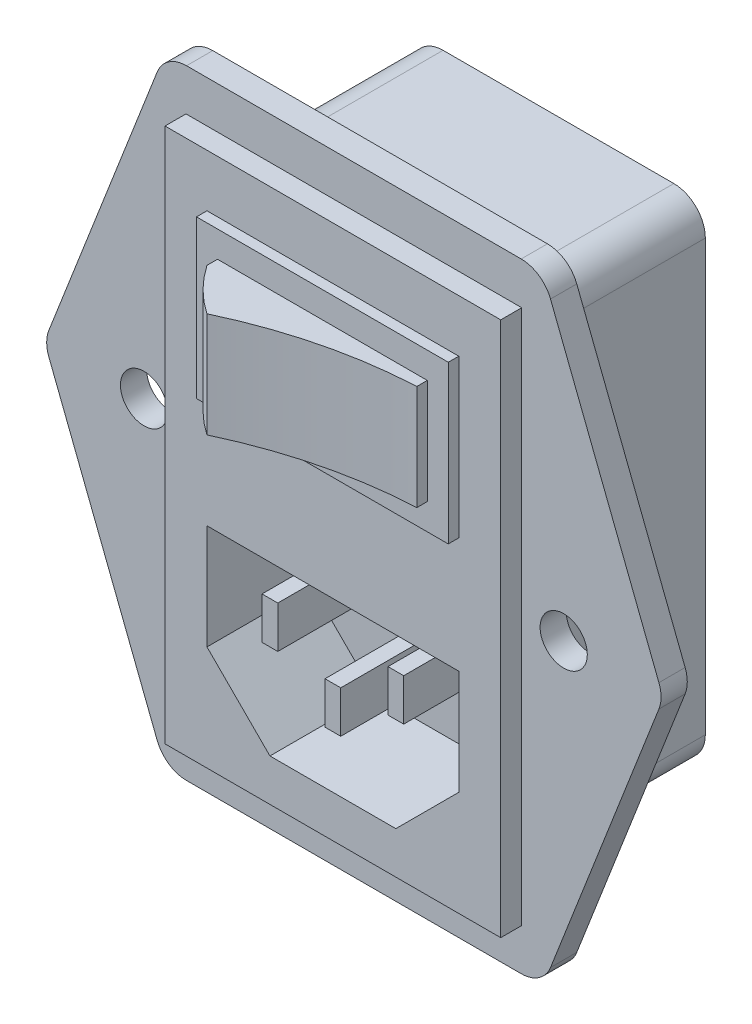
SolidWorks part; units mm, degrees
material "PBT Общее назначение"
ref_plane "Спереди" through (0, 0, 0) normal (0, 0, 1) x (1, 0, 0)
ref_plane "Сверху" through (0, 0, 0) normal (0, 1, 0) x (1, 0, 0)
ref_plane "Справа" through (0, 0, 0) normal (1, 0, 0) x (0, 0, -1)
sketch "Эскиз1" plane through (0, 0, 0) normal (0, 0, 1) x (1, 0, 0)
  line L0 (0, 0) -> (28, 0)
  line L1 (0, 0) -> (0, 47)
  line L2 (28, 0) -> (28, 47)
  line L3 (0, 47) -> (28, 47)
  dimension "D1" = 47
  dimension "D2" = 28
extrude "Бобышка-Вытянуть1" add sketch "Эскиз1" along normal blind 17
sketch "Эскиз2" plane through (0, 0, 17) normal (0, 0, 1) x (1, 0, 0)
  line L0 (14, 0) -> (14, 47) construction
  line L2 (0, 0) -> (28, 0) construction
  line L3 (28, 47) -> (0, 47) construction
  line L4 (-4, 53) -> (32, 53)
  line L5 (-4, 53) -> (-4, -6) construction
  line L6 (32, 53) -> (32, -6) construction
  line L7 (-4, -6) -> (32, -6)
  line L8 (-4, 53) -> (-15.5, 23.5)
  line L9 (-15.5, 23.5) -> (-4, -6)
  line L10 (14, 47) -> (14, 53) construction
  line L11 (43.5, 23.5) -> (32, -6)
  line L12 (32, 53) -> (43.5, 23.5)
  line L13 (0, 23.5) -> (28, 23.5) construction
  line L14 (0, 47) -> (0, 0) construction
  line L15 (28, 0) -> (28, 47) construction
  line L16 (-15.5, 23.5) -> (43.5, 23.5) construction
  line L17 (-4, 23.5) -> (32, 23.5) construction
  dimension "D1" = 59
  dimension "D2" = 59
  dimension "D3" = 6
  dimension "D4" = 4
extrude "Бобышка-Вытянуть2" add sketch "Эскиз2" along normal blind 2.5
sketch "Эскиз3" plane through (0, 0, 19.5) normal (0, 0, 1) x (1, 0, 0)
  line L0 (-2, 49) -> (30, 49)
  line L1 (-2, 49) -> (-2, -2)
  line L2 (30, 49) -> (30, -2)
  line L3 (-2, -2) -> (30, -2)
  line L4 (14, 47) -> (14, 0) construction
  line L5 (28, 23.5) -> (0, 23.5) construction
  line L8 (0, 47) -> (0, 0)
  line L9 (28, 47) -> (0, 47)
  line L10 (28, 0) -> (28, 47)
  line L11 (0, 0) -> (28, 0)
  line L12 (0, 47) -> (0, 0) construction
  line L13 (28, 47) -> (0, 47) construction
  line L14 (28, 0) -> (28, 47) construction
  line L15 (0, 0) -> (28, 0) construction
  dimension "D2" = 2
  dimension "D3" = 2
  dimension "D4" = 2
  dimension "D5" = 2
  dimension "D1" = 0
extrude "Бобышка-Вытянуть3" add sketch "Эскиз3" along normal blind 2
sketch "Эскиз5" plane through (0, 0, 21.5) normal (0, 0, 1) x (1, 0, 0)
  line L0 (2, 18) -> (26, 18)
  line L1 (2, 18) -> (2, 8)
  line L2 (26, 18) -> (26, 8)
  line L3 (2, 8) -> (26, 8) construction
  line L4 (14, 49) -> (14, -2) construction
  line L5 (30, 49) -> (-2, 49) construction
  line L6 (-2, -2) -> (30, -2) construction
  line L7 (14, 18) -> (14, 8) construction
  line L8 (2, 8) -> (8, 2)
  line L9 (8, 2) -> (20, 2)
  line L10 (26, 8) -> (20, 2)
  line L11 (8, 2) -> (8, 18) construction
  line L12 (7.25, 15) -> (8.75, 15)
  line L13 (7.25, 15) -> (7.25, 11)
  line L14 (8.75, 15) -> (8.75, 11)
  line L15 (7.25, 11) -> (8.75, 11)
  line L16 (13.25, 11) -> (14.75, 11)
  line L17 (13.25, 11) -> (13.25, 7)
  line L18 (14.75, 11) -> (14.75, 7)
  line L19 (13.25, 7) -> (14.75, 7)
  line L20 (20.75, 11) -> (19.25, 11)
  line L21 (19.25, 15) -> (19.25, 11)
  line L22 (20.75, 15) -> (20.75, 11)
  line L23 (20.75, 15) -> (19.25, 15)
  point P14 (8, 15)
  point P15 (14, 2)
  point P19 (14, 11)
  point P30 (20, 15)
  dimension "D1" = 24
  dimension "D2" = 45
  dimension "D3" = 16
  dimension "D4" = 6
  dimension "D5" = 4
  dimension "D6" = 4
  dimension "D7" = 1.5
  dimension "D8" = 3
  dimension "D9" = 4
  dimension "D10" = 1.5
extrude "Вырез-Вытянуть3" cut sketch "Эскиз5" against normal blind 10
sketch "Эскиз6" plane through (0, 0, 21.5) normal (0, 0, 1) x (1, 0, 0)
  line L0 (2, 44) -> (26, 44)
  line L1 (2, 44) -> (2, 29)
  line L2 (26, 44) -> (26, 29)
  line L3 (2, 29) -> (26, 29)
  line L4 (14, 49) -> (14, -2) construction
  line L5 (30, 49) -> (-2, 49) construction
  line L6 (-2, -2) -> (30, -2) construction
  point P10 (14, 44)
  dimension "D1" = 15
  dimension "D2" = 24
  dimension "D3" = 5
extrude "Бобышка-Вытянуть4" add sketch "Эскиз6" along normal blind 1
sketch "Эскиз7" plane through (0, 0, 22.5) normal (0, 0, 1) x (1, 0, 0)
  line L0 (4, 41.5) -> (24, 41.5)
  line L1 (4, 41.5) -> (4, 31.5)
  line L2 (24, 41.5) -> (24, 31.5)
  line L3 (4, 31.5) -> (24, 31.5)
  line L4 (14, 44) -> (14, 29) construction
  line L5 (26, 44) -> (2, 44) construction
  line L6 (2, 29) -> (26, 29) construction
  line L7 (26, 36.5) -> (2, 36.5) construction
  line L8 (26, 29) -> (26, 44) construction
  line L9 (2, 44) -> (2, 29) construction
  point P16 (4, 36.5)
  point P17 (14, 41.5)
  dimension "D1" = 10
  dimension "D2" = 20
extrude "Бобышка-Вытянуть5" add sketch "Эскиз7" along normal blind 1
sketch "Эскиз8" plane through (0, 31.5, 0) normal (0, -1, 0) x (1, 0, 0)
  line L0 (4, 23.5) -> (24, 23.5) construction
  line L1 (4, 23.5) -> (24, 23.5)
  line L5 (8, 27.5) -> (8, 23.5) construction
  arc A0 (8, 27.5) -> (4, 23.5) centre (16.4163, 15.0837) ccw
  arc A1 (8, 27.5) -> (24, 23.5) centre (25.9882, 65.4529) ccw
  dimension "D2" = 15
  dimension "D3" = 42
  dimension "D1" = 4
  dimension "D4" = 4
extrude "Бобышка-Вытянуть6" add sketch "Эскиз8" against normal up to surface (10 mm away) up to face at (14, 41.5, 23)
sketch "Эскиз9" plane through (0, 0, 19.5) normal (0, 0, 1) x (1, 0, 0)
  line L0 (-15.5, 23.5) -> (43.5, 23.5) construction
  line L1 (14, 53) -> (14, -6) construction
  line L2 (32, 53) -> (-4, 53) construction
  line L3 (-4, -6) -> (32, -6) construction
  circle A0 centre (-6, 23.5) radius 2.25
  circle A1 centre (34, 23.5) radius 2.25
  dimension "D1" = 4.5
  dimension "D2" = 40
  dimension "D3" = 20
extrude "Вырез-Вытянуть4" cut sketch "Эскиз9" against normal through all
fillet "Скругление1" radius 3 10 edges at (-4, -6, 18.25) (32, -6, 18.25) (43.5, 23.5, 18.25) (32, 53, 18.25) (-4, 53, 18.25) (-15.5, 23.5, 18.25) (0, 0, 8.5) (28, 0, 8.5) (0, 47, 8.5) (28, 47, 8.5)
